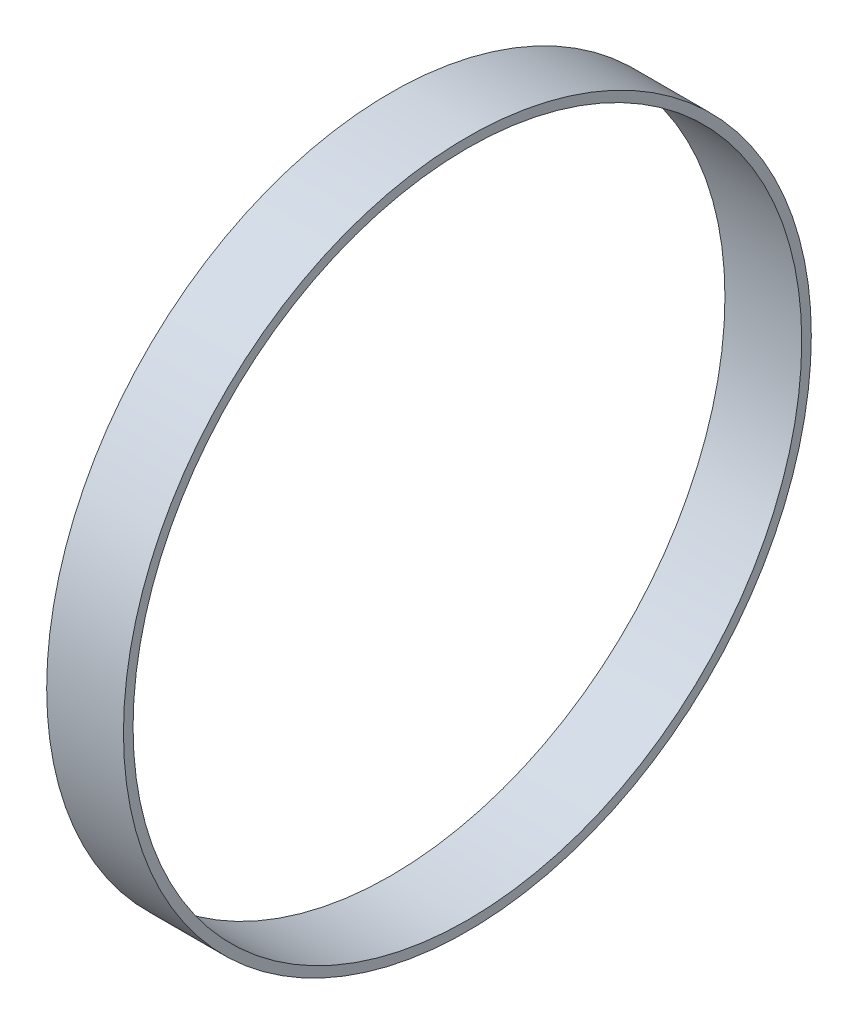
SolidWorks part; units mm, degrees
material "AISI 1020"
ref_plane "Спереди" through (0, 0, 0) normal (0, 0, 1) x (1, 0, 0)
ref_plane "Сверху" through (0, 0, 0) normal (0, 1, 0) x (1, 0, 0)
ref_plane "Справа" through (0, 0, 0) normal (1, 0, 0) x (0, 0, -1)
sketch "Эскиз1" plane through (0, 0, 0) normal (0, 0, 1) x (1, 0, 0)
  line L0 (0, 0) -> (-219.8744, 0) construction
  line L2 (0, 107.5) -> (-24, 107.5)
  line L3 (0, 107.5) -> (0, 104.5)
  line L4 (0, 104.5) -> (-24, 104.5)
  line L5 (-24, 107.5) -> (-24, 104.5)
  dimension "D1" = 209
  dimension "D2" = 215
  dimension "D3" = 24
revolve "Повернуть1" add sketch "Эскиз1" angle 360 about L0
